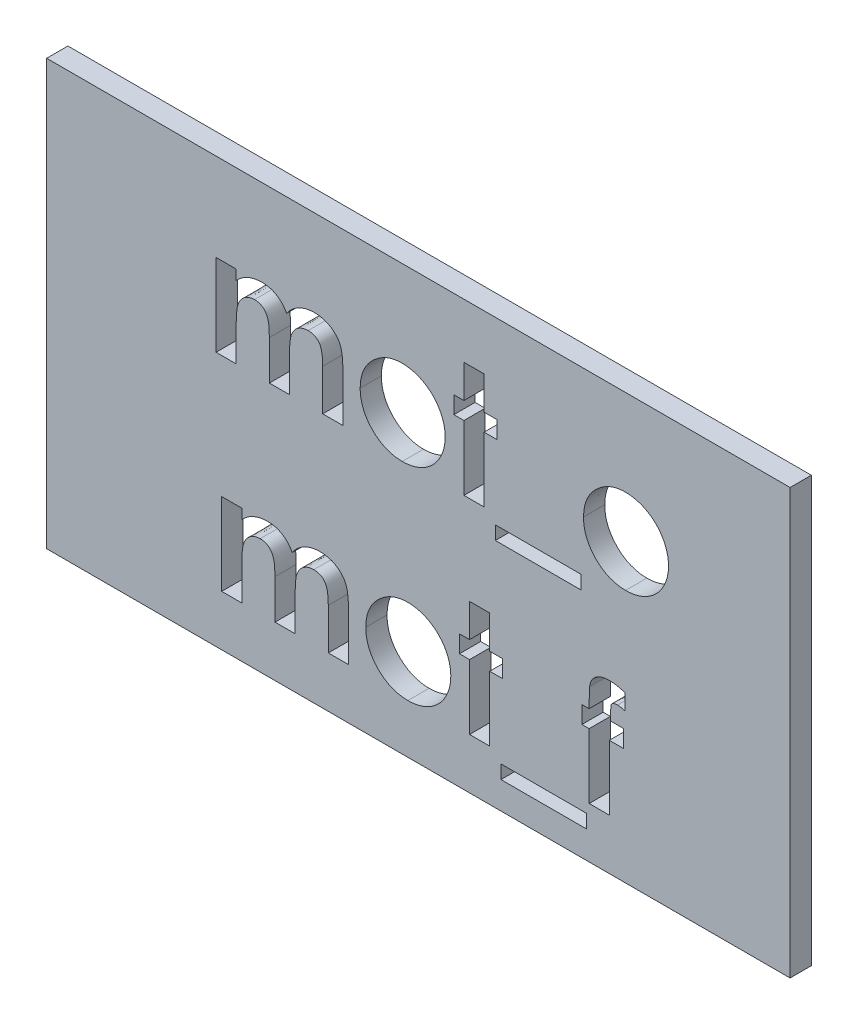
SolidWorks part; units mm, degrees
ref_plane "Plan de face" through (0, 0, 0) normal (0, 0, 1) x (1, 0, 0)
ref_plane "Plan de dessus" through (0, 0, 0) normal (0, 1, 0) x (1, 0, 0)
ref_plane "Plan de droite" through (0, 0, 0) normal (1, 0, 0) x (0, 0, -1)
sketch "Esquisse1" plane through (0, 0, 0) normal (0, 0, 1) x (1, 0, 0)
  line L1 (0, 0) -> (35, 0)
  line L2 (0, 0) -> (0, -20)
  line L3 (0, -20) -> (35, -20)
  line L4 (35, 0) -> (35, -20)
  dimension "D1" = 35
  dimension "D2" = 20
extrude "Boss.-Extru.1" add sketch "Esquisse1" along normal blind 1
sketch "Esquisse2" plane through (0, 0, 0) normal (0, 0, -1) x (-1, 0, 0)
  line L0 (-35, 0) -> (0, 0) construction
  line L1 (-35, -20) -> (-35, 0) construction
  line L2 (0, 0) -> (0, -20) construction
  circle A0 centre (-30, -5) radius 1
  circle A1 centre (-5, -5) radius 1
  dimension "D4" = 2
  dimension "D1" = 5
  dimension "D2" = 5
  dimension "D3" = 5
extrude "Boss.-Extru.2" add sketch "Esquisse2" along normal blind 3
chamfer "Chanfrein1" distance 0.5 angle 45 2 edges at (29, -5, -3) (4, -5, -3)
sketch "Esquisse3" plane through (0, 0, 1) normal (0, 0, 1) x (1, 0, 0)
  line L0 (7.5, -8) -> (27.5, -8) construction
  line L1 (35, 0) -> (0, 0) construction
  line L3 (0, -20) -> (35, -20) construction
  line L4 (0, 0) -> (0, -20) construction
  line L5 (35, -20) -> (35, 0) construction
  text T1 "<b>mot_o</b>\r\n<b>mot_f</b>" font "Century Gothic" height in points 20
  point P12 (27.5, -8)
  dimension "D1" = 12
  dimension "D2" = 7.5
  dimension "D3" = 20
  dimension "D4" = 7.5
  dimension "D5" = 8
extrude "Enlèv. mat.-Extru.2" cut sketch "Esquisse3" against normal blind 1
sketch "Esquisse5" plane through (0, 0, 1) normal (0, 0, 1) x (1, 0, 0)
  line L14 (21.1219, -9.0998) -> (25.1532, -9.0998)
  line L15 (21.1219, -8.4606) -> (21.1219, -9.0998)
  line L16 (25.1532, -8.4606) -> (21.1219, -8.4606)
  line L17 (25.1532, -9.0998) -> (25.1532, -8.4606)
  line L18 (21.1219, -9.0998) -> (25.1532, -9.0998)
  line L19 (21.1219, -8.4606) -> (21.1219, -9.0998)
  line L20 (25.1532, -8.4606) -> (21.1219, -8.4606)
  line L21 (25.1532, -9.0998) -> (25.1532, -8.4606)
  line L26 (21.3866, -18.7157) -> (25.4179, -18.7157)
  line L27 (21.3866, -18.0765) -> (21.3866, -18.7157)
  line L28 (25.4179, -18.0765) -> (21.3866, -18.0765)
  line L29 (25.4179, -18.7157) -> (25.4179, -18.0765)
  line L30 (21.3866, -18.7157) -> (25.4179, -18.7157)
  line L31 (21.3866, -18.0765) -> (21.3866, -18.7157)
  line L32 (25.4179, -18.0765) -> (21.3866, -18.0765)
  line L33 (25.4179, -18.7157) -> (25.4179, -18.0765)
  dimension "D1" = 0.15
  dimension "D2" = 0.15
extrude "Enlèv. mat.-Extru.3" cut sketch "Esquisse5" against normal through all
